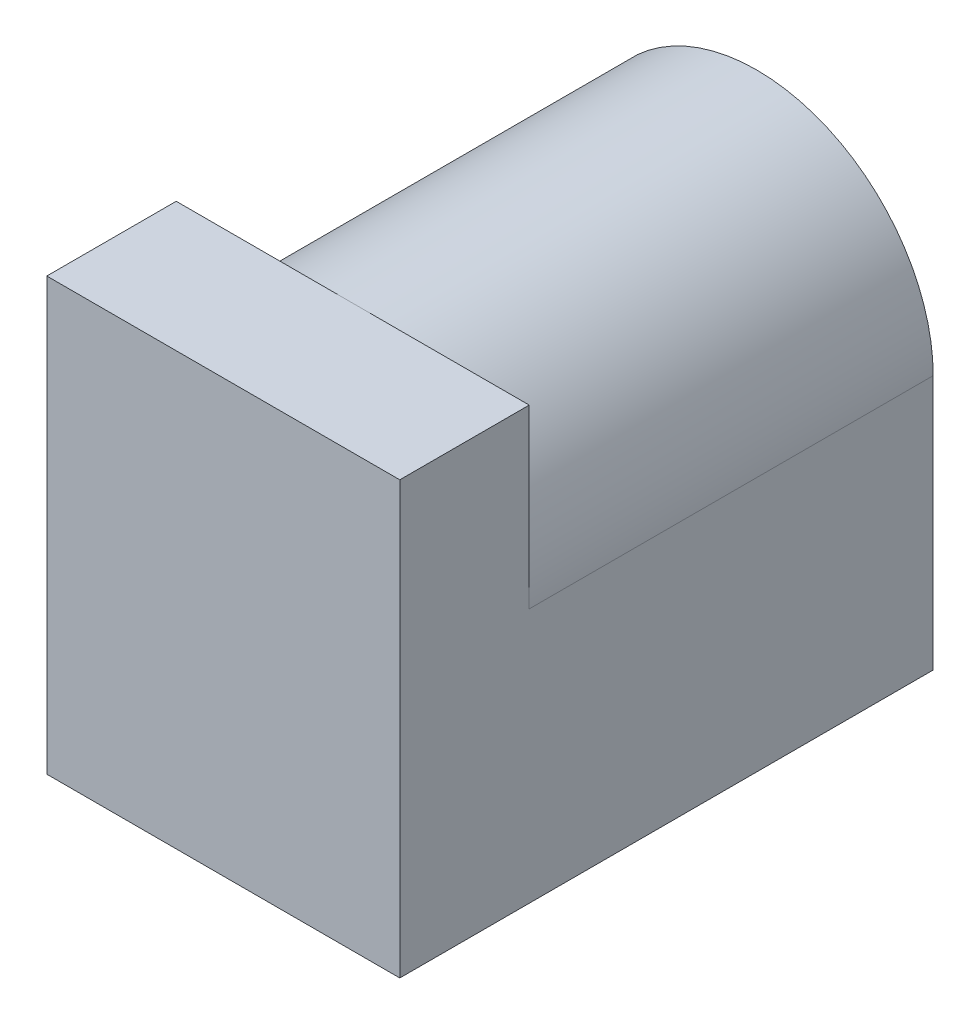
SolidWorks part; units mm, degrees
ref_plane "Front Plane" through (0, 0, 0) normal (0, 0, 1) x (1, 0, 0)
ref_plane "Top Plane" through (0, 0, 0) normal (0, 1, 0) x (1, 0, 0)
ref_plane "Right Plane" through (0, 0, 0) normal (1, 0, 0) x (0, 0, -1)
sketch "Sketch1" plane through (0, 0, 0) normal (0, 0, 1) x (1, 0, 0)
  line L1 (-4.5, -5.5) -> (4.5, -5.5)
  line L2 (-4.5, -5.5) -> (-4.5, 5.5)
  line L3 (-4.5, 5.5) -> (4.5, 5.5)
  line L4 (4.5, -5.5) -> (4.5, 5.5)
  line L5 (-4.5, -5.5) -> (4.5, 5.5) construction
  line L6 (-4.5, 5.5) -> (4.5, -5.5) construction
  point P0 (0, 0)
  dimension "D1" = 11
  dimension "D2" = 9
extrude "Boss-Extrude1" add sketch "Sketch1" along normal blind 3.3
sketch "Sketch2" plane through (0, 0, 0) normal (0, 0, -1) x (-1, 0, 0)
  line L0 (4.5, -5.5) -> (-4.5, -5.5) construction
  line L1 (-5.5787, 1) -> (-4.5, 1) construction
  line L2 (4.5, 1) -> (6.8024, 1) construction
  line L4 (-4.5, 1) -> (-4.5, -5.5)
  line L5 (-4.5, -5.5) -> (4.5, -5.5)
  line L6 (4.5, 1) -> (4.5, -5.5)
  line L7 (-4.5, 1) -> (4.5, -5.5) construction
  line L8 (-4.5, -5.5) -> (4.5, 1) construction
  arc A0 (4.5, 1) -> (-4.5, 1) centre (0, 1) ccw
  point P4 (0, -5.5)
  point P11 (0, -2.25)
  dimension "D1" = 9
  dimension "D2" = 6.5
extrude "Boss-Extrude2" add sketch "Sketch2" along normal blind 10.3
